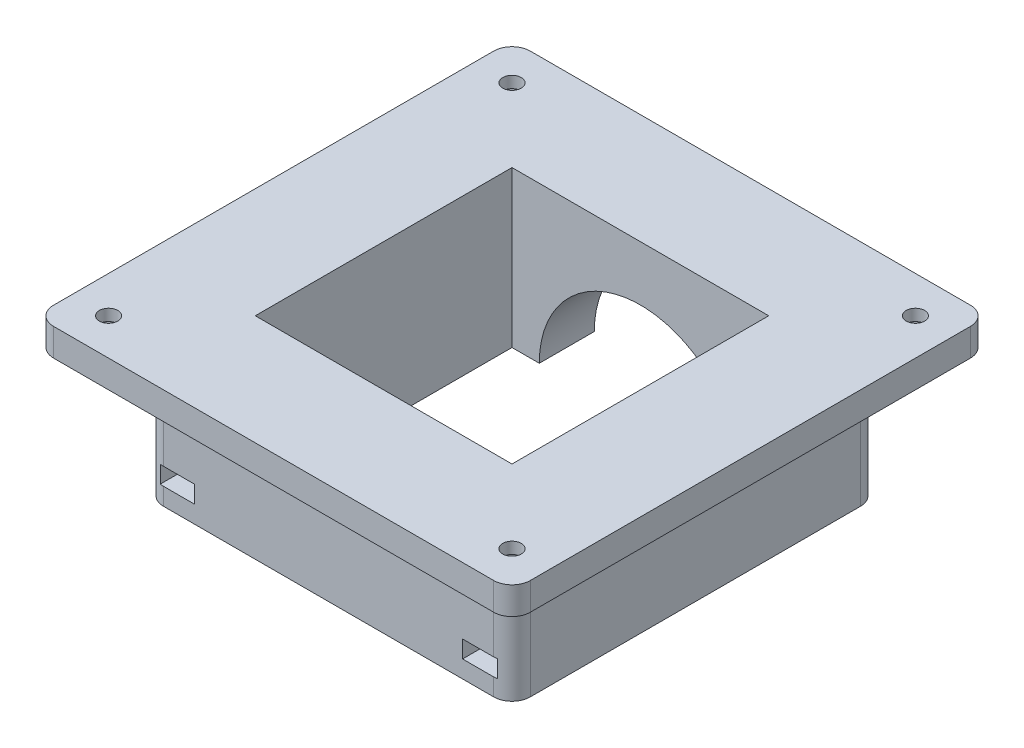
SolidWorks part; units mm, degrees
ref_plane "Front Plane" through (0, 0, 0) normal (0, 0, 1) x (1, 0, 0)
ref_plane "Top Plane" through (0, 0, 0) normal (0, 1, 0) x (1, 0, 0)
ref_plane "Right Plane" through (0, 0, 0) normal (1, 0, 0) x (0, 0, -1)
sketch "Sketch1" plane through (0, 0, 0) normal (0, 1, 0) x (1, 0, 0)
  line L0 (-34.925, 34.925) -> (-34.925, -34.925) construction
  line L1 (-41.275, -41.275) -> (41.275, -41.275)
  line L2 (-41.275, -41.275) -> (-41.275, 41.275)
  line L3 (-41.275, 41.275) -> (41.275, 41.275)
  line L4 (41.275, -41.275) -> (41.275, 41.275)
  line L5 (-41.275, -41.275) -> (41.275, 41.275) construction
  line L6 (-41.275, 41.275) -> (41.275, -41.275) construction
  line L7 (-34.925, -34.925) -> (34.925, -34.925) construction
  line L8 (34.925, -34.925) -> (34.925, 34.925) construction
  line L10 (-22.225, 22.225) -> (22.225, 22.225)
  line L11 (-22.225, 22.225) -> (-22.225, -22.225)
  line L12 (-22.225, -22.225) -> (22.225, -22.225)
  line L13 (22.225, 22.225) -> (22.225, -22.225)
  line L14 (-22.225, 22.225) -> (22.225, -22.225) construction
  line L15 (-22.225, -22.225) -> (22.225, 22.225) construction
  circle A0 centre (-34.925, 34.925) radius 1.6
  circle A1 centre (34.925, 34.925) radius 1.6
  circle A2 centre (34.925, -34.925) radius 1.6
  circle A3 centre (-34.925, -34.925) radius 1.6
  circle A4 centre (0, 0) radius 22.225 construction
  point P0 (0, 0)
  dimension "D2" = 3.2
  dimension "D4" = 44.45
  dimension "D1" = 69.85
  dimension "D3" = 6.35
extrude "Boss-Extrude1" add sketch "Sketch1" along normal blind 4.7625
sketch "Sketch2" plane through (0, 0, 0) normal (0, -1, 0) x (1, 0, 0)
  line L0 (22.225, -22.225) -> (-22.225, -22.225) construction
  line L1 (-31.75, -31.75) -> (31.75, -31.75)
  line L2 (-31.75, -31.75) -> (-31.75, 31.75)
  line L3 (-31.75, 31.75) -> (31.75, 31.75)
  line L4 (31.75, -31.75) -> (31.75, 31.75)
  line L5 (-31.75, -31.75) -> (31.75, 31.75) construction
  line L6 (-31.75, 31.75) -> (31.75, -31.75) construction
  line L7 (-22.225, -22.225) -> (-22.225, 22.225) construction
  line L8 (-22.225, 22.225) -> (22.225, 22.225) construction
  line L9 (22.225, 22.225) -> (22.225, -22.225) construction
  line L10 (22.225, -22.225) -> (-22.225, -22.225)
  line L11 (-22.225, -22.225) -> (-22.225, 22.225)
  line L12 (-22.225, 22.225) -> (22.225, 22.225)
  line L13 (22.225, 22.225) -> (22.225, -22.225)
  point P0 (0, 0)
  dimension "D1" = 63.5
extrude "Boss-Extrude2" add sketch "Sketch2" along normal blind 6.35
sketch "Sketch3" plane through (0, -6.35, 0) normal (0, -1, 0) x (1, 0, 0)
  line L1 (22.225, -22.225) -> (-22.225, -22.225)
  line L2 (22.225, -22.225) -> (22.225, 22.225)
  line L3 (22.225, 22.225) -> (-22.225, 22.225)
  line L4 (31.75, -31.75) -> (31.75, 31.75)
  line L5 (31.75, 31.75) -> (-31.75, 31.75)
  line L6 (-31.75, 31.75) -> (-31.75, -31.75)
  line L7 (-31.75, -31.75) -> (31.75, -31.75)
  line L8 (31.75, -31.75) -> (31.75, 31.75)
  line L9 (31.75, 31.75) -> (-31.75, 31.75)
  line L10 (-31.75, 31.75) -> (-31.75, -31.75)
  line L11 (-31.75, -31.75) -> (31.75, -31.75)
  line L12 (-22.225, -22.225) -> (-22.225, 22.225)
  line L13 (22.225, -22.225) -> (-22.225, 22.225) construction
  line L14 (22.225, 22.225) -> (-22.225, -22.225) construction
  point P2 (0, 0)
  dimension "D1" = 0
extrude "Boss-Extrude3" add sketch "Sketch3" along normal blind 15.875
sketch "Sketch4" plane through (0, 0, -31.75) normal (0, 0, -1) x (-1, 0, 0)
  line L0 (31.75, -22.225) -> (-31.75, -22.225) construction
  circle A0 centre (0, -22.225) radius 17.5
  dimension "D1" = 35
extrude "Cut-Extrude1" cut sketch "Sketch4" against normal up to surface (31.75 mm away) up to plane "Front Plane"
fillet "Fillet1" radius 3.175 8 edges at (41.275, 2.3813, 41.275) (31.75, -11.1125, 31.75) (41.275, 2.3813, -41.275) (31.75, -11.1125, -31.75) (-31.75, -11.1125, 31.75) (-31.75, -11.1125, -31.75) (-41.275, 2.3813, -41.275) (-41.275, 2.3813, 41.275)
sketch "Sketch5" plane through (0, -22.225, 0) normal (0, -1, 0) x (1, 0, 0)
  line L0 (-31.75, -26.1938) -> (-26.1938, -26.1938) construction
  line L1 (-24.6938, -28.7918) -> (-23.1938, -27.9258) construction
  line L2 (-23.1938, -27.9258) -> (-23.1938, -24.4617)
  line L3 (-23.1938, -24.4617) -> (-26.1937, -22.7296)
  line L4 (-26.1937, -22.7296) -> (-29.1937, -24.4617)
  line L5 (-29.1937, -24.4617) -> (-29.1937, -27.9258)
  line L6 (-29.1937, -27.9258) -> (-27.6938, -28.7918) construction
  line L7 (-31.75, 28.575) -> (-31.75, -28.575) construction
  line L8 (-26.1938, -26.1938) -> (-26.1938, -31.75) construction
  line L9 (-28.575, -31.75) -> (-17.5, -31.75) construction
  line L10 (-29.1937, -27.9258) -> (-29.1937, -31.75)
  line L11 (-29.1937, -31.75) -> (-23.1938, -31.75)
  line L12 (-23.1938, -31.75) -> (-23.1938, -27.9258)
  line L13 (-27.6938, -28.7918) -> (-26.1937, -29.6579) construction
  line L14 (-26.1937, -29.6579) -> (-24.6938, -28.7918) construction
  arc A0 (-23.1938, -26.1938) -> (-29.1938, -26.1938) centre (-26.1938, -26.1938) ccw construction
  arc A1 (-27.6938, -28.7918) -> (-26.1938, -29.1937) centre (-26.1938, -26.1938) ccw construction
  arc A2 (-26.1938, -29.1937) -> (-24.6938, -28.7918) centre (-26.1938, -26.1938) ccw construction
  arc A3 (-24.6938, -28.7918) -> (-23.1938, -26.1938) centre (-26.1938, -26.1938) ccw construction
  arc A4 (-29.1938, -26.1938) -> (-27.6938, -28.7918) centre (-26.1938, -26.1938) ccw construction
  dimension "D1" = 6
  dimension "D2" = 5.5562
extrude "Cut-Extrude3" cut sketch "Sketch5" against normal blind 3 from offset 3 offset against normal yes
sketch "Sketch6" plane through (0, -16.225, 0) normal (0, -1, 0) x (-1, 0, 0)
  line L0 (23.1938, 24.4617) -> (26.1937, 26.1938) construction
  line L1 (26.1937, 26.1938) -> (26.1937, 22.7296) construction
  circle A0 centre (26.1937, 26.1938) radius 1.6
  dimension "D1" = 3.2
extrude "Cut-Extrude4" cut sketch "Sketch6" along normal through all
mirror "Mirror1" about plane through (0, 0, 0) normal (1, 0, 0) of "Cut-Extrude3", "Cut-Extrude4"
mirror "Mirror2" about plane through (0, 0, 0) normal (0, 0, 1) of "Mirror1", "Cut-Extrude4", "Cut-Extrude3"
sketch "Sketch7" plane through (0, 0, 0) normal (0, -1, 0) x (-1, 0, 0)
  line L0 (26.1937, -22.7296) -> (29.1937, -24.4617) construction
  line L1 (34.925, -31.4609) -> (31.925, -33.1929)
  line L2 (31.925, -33.1929) -> (31.925, -36.6571)
  line L3 (31.925, -36.6571) -> (34.925, -38.3891)
  line L4 (34.925, -38.3891) -> (37.925, -36.6571)
  line L5 (37.925, -36.6571) -> (37.925, -33.1929)
  line L6 (37.925, -33.1929) -> (34.925, -31.4609)
  line L7 (-37.925, -33.1929) -> (-37.925, -36.6571)
  line L8 (-37.925, -36.6571) -> (-34.925, -38.3891)
  line L9 (-34.925, -38.3891) -> (-31.925, -36.6571)
  line L10 (-31.925, -36.6571) -> (-31.925, -33.1929)
  line L11 (-31.925, -33.1929) -> (-34.925, -31.4609)
  line L12 (-34.925, -31.4609) -> (-37.925, -33.1929)
  line L13 (-37.925, 36.6571) -> (-37.925, 33.1929)
  line L14 (-37.925, 33.1929) -> (-34.925, 31.4609)
  line L15 (-34.925, 31.4609) -> (-31.925, 33.1929)
  line L16 (-31.925, 33.1929) -> (-31.925, 36.6571)
  line L17 (-31.925, 36.6571) -> (-34.925, 38.3891)
  line L18 (-34.925, 38.3891) -> (-37.925, 36.6571)
  line L19 (31.925, 36.6571) -> (31.925, 33.1929)
  line L20 (31.925, 33.1929) -> (34.925, 31.4609)
  line L21 (34.925, 31.4609) -> (37.925, 33.1929)
  line L22 (37.925, 33.1929) -> (37.925, 36.6571)
  line L23 (37.925, 36.6571) -> (34.925, 38.3891)
  line L24 (34.925, 38.3891) -> (31.925, 36.6571)
  circle A0 centre (34.925, -34.925) radius 3 construction
  circle A1 centre (-34.925, -34.925) radius 3 construction
  circle A2 centre (-34.925, 34.925) radius 3 construction
  circle A3 centre (34.925, 34.925) radius 3 construction
extrude "Cut-Extrude5" cut sketch "Sketch7" against normal offset from surface (2.7625 mm away) 2 up to face at (-34.925, 4.7625, 36.525)
